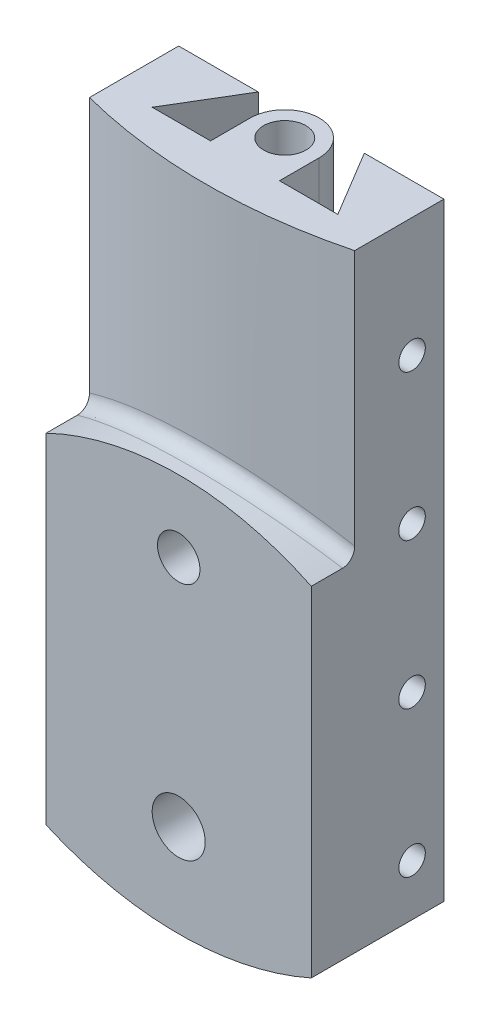
SolidWorks part; units mm, degrees
material "Plain Carbon Steel"
ref_plane "Front Plane" through (0, 0, 0) normal (0, 0, 1) x (1, 0, 0)
ref_plane "Top Plane" through (0, 0, 0) normal (0, 1, 0) x (1, 0, 0)
ref_plane "Right Plane" through (0, 0, 0) normal (1, 0, 0) x (0, 0, -1)
sketch "Sketch1" plane through (0, 0, 0) normal (0, 0, 1) x (1, 0, 0)
  line L1 (-50, -120) -> (50, -120)
  line L2 (-50, -120) -> (-50, 120)
  line L3 (-50, 120) -> (50, 120)
  line L4 (50, -120) -> (50, 120)
  line L5 (-50, -120) -> (50, 120) construction
  line L6 (-50, 120) -> (50, -120) construction
  circle A0 centre (0, 3) radius 8
  circle A1 centre (0, -85) radius 10
  point P0 (0, 0)
  point P11 (0, -120)
  dimension "D3" = 16
  dimension "D4" = 20
  dimension "D1" = 240
  dimension "D2" = 100
  dimension "D5" = 117
  dimension "D6" = 88
extrude "Boss-Extrude1" add sketch "Sketch1" along normal mid plane 50
sketch "Sketch2" plane through (0, 0, 25) normal (0, 0, 1) x (1, 0, 0)
  line L0 (50, -120) -> (50, 120) construction
  line L1 (-50, -120) -> (50, -120) construction
  line L2 (-50, 120) -> (-50, -120) construction
  line L3 (50, -120) -> (50, 18.5616)
  line L4 (-50, -120) -> (50, -120)
  line L5 (-50, 18.5616) -> (-50, -120)
  arc A0 (50, 18.5616) -> (-50, 18.5616) centre (0, -85) ccw
  circle A1 centre (0, -85) radius 10 construction
  circle A2 centre (0, 3) radius 8 construction
  circle A3 centre (0, -85) radius 10
  circle A4 centre (0, 3) radius 8
  dimension "D1" = 115
extrude "Cut-Extrude1" cut sketch "Sketch2" against normal blind 10 flip side to cut
sketch "Sketch3" plane through (0, 0, 25) normal (0, 0, 1) x (1, 0, 0)
  line L0 (-50, -120) -> (50, -120) construction
  line L1 (0, 148.2762) -> (0, -148.2762) construction
  line L4 (50, -120) -> (50, 18.5616) construction
  line L5 (-50, 18.5616) -> (-50, -120) construction
  line L6 (50, 120) -> (-50, 120)
  line L9 (50, -109.3788) -> (50, 120)
  line L10 (-50, 120) -> (-50, -109.3788)
  arc A1 (-50, -109.3788) -> (50, -109.3788) centre (0, 3) ccw
  point P20 (0, 0)
  dimension "D1" = 123
extrude "Cut-Extrude2" cut sketch "Sketch3" against normal up to next flip side to cut
sketch "Sketch7" plane through (0, 120, 0) normal (0, 1, 0) x (1, 0, 0)
  line L0 (-35, 0) -> (35, 0)
  line L1 (35, 0) -> (20, 25)
  line L2 (50, 25) -> (-50, 25) construction
  line L3 (20, 25) -> (-20, 25)
  line L4 (-20, 25) -> (-35, 0)
  line L5 (0, 0) -> (0, 32.1639) construction
  point P4 (0, 0)
  dimension "D1" = 40
  dimension "D2" = 70
extrude "Cut-Extrude7" cut sketch "Sketch7" against normal up to next
sketch "Sketch8" plane through (0, 120, 0) normal (0, 1, 0) x (1, 0, 0)
  line L0 (13, 15) -> (13, 0)
  line L1 (-35, 0) -> (35, 0) construction
  line L2 (13, 0) -> (-13, 0)
  line L3 (-13, 0) -> (-13, 15)
  line L4 (0, 0) -> (0, 36.3944) construction
  arc A0 (13, 15) -> (-13, 15) centre (0, 15) ccw
  circle A1 centre (0, 15) radius 8
  dimension "D1" = 13
  dimension "D2" = 16
  dimension "D3" = 15
extrude "Boss-Extrude2" add sketch "Sketch8" against normal blind 30
sketch "Sketch9" plane through (0, 120, 0) normal (0, 1, 0) x (1, 0, 0)
  line L0 (-50, -15) -> (-50, 25) construction
  line L1 (50, -15) -> (50, 25) construction
  line L2 (50, -15) -> (-50, -15) construction
  line L3 (50, -8.6492) -> (50, -25)
  line L4 (50, -25) -> (-50, -25)
  line L5 (-50, -25) -> (-50, -8.6492)
  arc A0 (-50, -8.6492) -> (50, -8.6492) centre (0, 185) ccw
  dimension "D1" = 200
extrude "Cut-Extrude8" cut sketch "Sketch9" against normal up to surface (101.4384 mm away)
sketch "Sketch10" plane through (50, 0, 0) normal (1, 0, 0) x (0, 0, -1)
  line L0 (25, -109.3788) -> (25, 120) construction
  line L1 (-8.6492, 120) -> (25, 120) construction
  circle A0 centre (13, -90) radius 5
  dimension "D1" = 10
  dimension "D2" = 12
  dimension "D3" = 210
extrude "Cut-Extrude9" cut sketch "Sketch10" against normal up to next
pattern_linear "LPattern1" count 4 spacing 55 along (0, 1, 0) of "Cut-Extrude9"
mirror "Mirror1" about plane through (0, 0, 0) normal (1, 0, 0) of "LPattern1", "Cut-Extrude9"
fillet "Fillet1" radius 5 1 edges at (-17.181, 28.7093, 14.2607)
